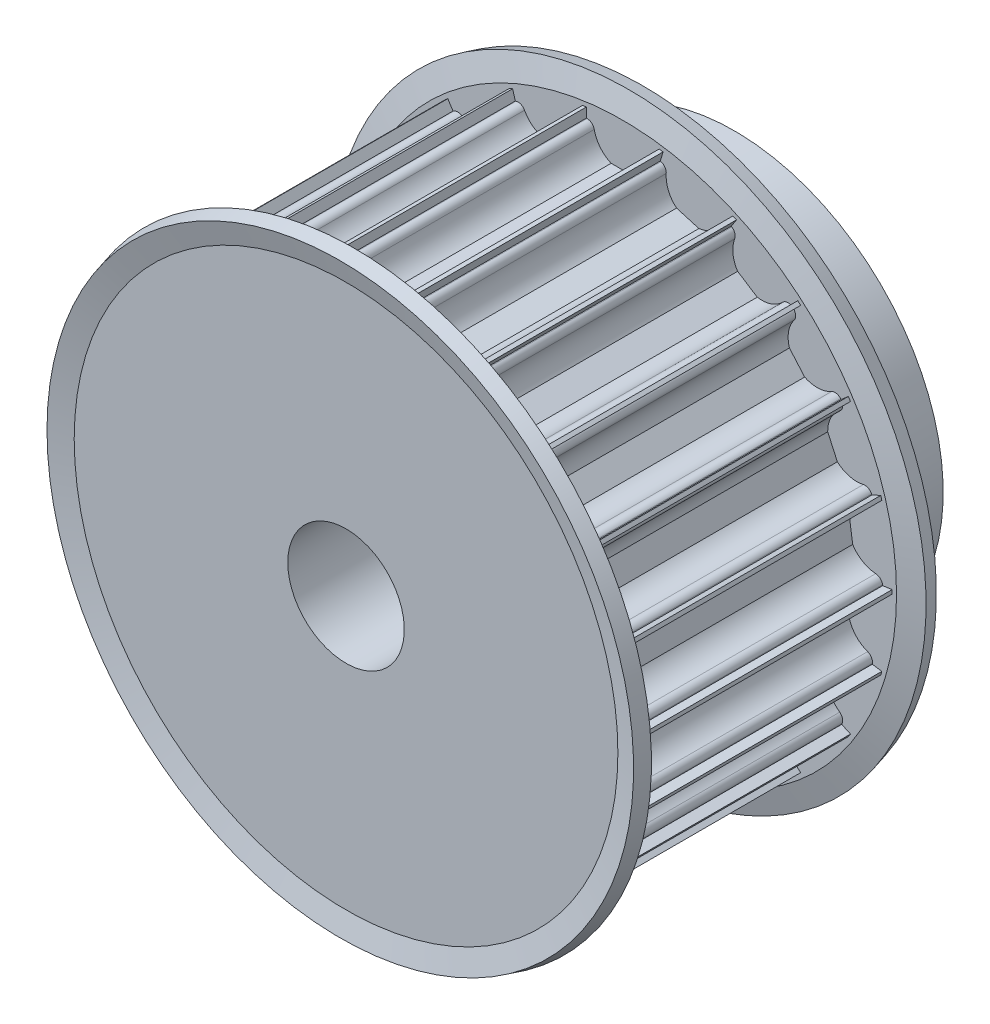
SolidWorks part; units mm, degrees
ref_plane "Front Plane" through (0, 0, 0) normal (0, 0, 1) x (1, 0, 0)
ref_plane "Top Plane" through (0, 0, 0) normal (0, 1, 0) x (1, 0, 0)
ref_plane "Right Plane" through (0, 0, 0) normal (1, 0, 0) x (0, 0, -1)
ref_axis "Axis1" through (0, 0, -88.99) along (0, 0, 1)
sketch "Sketch1" plane through (0, 0, 0) normal (1, 0, 0) x (0, 0, -1)
  line L0 (0, 6) -> (0, 27.75)
  line L1 (0, 27.75) -> (30, 27.75)
  line L2 (30, 27.75) -> (30, 21.5)
  line L3 (30, 21.5) -> (40, 21.5)
  line L4 (40, 21.5) -> (40, 6)
  line L5 (40, 6) -> (0, 6)
  line L6 (88.99, 0) -> (-88.99, 0) construction
  dimension "D1" = 21.75
  dimension "D2" = 30
  dimension "D3" = 10
  dimension "D4" = 15.5
  dimension "D5" = 6
revolve "Revolve1" add sketch "Sketch1" angle 360 about axis through (0, 0, -88.99) along (0, 0, 1)
sketch "Sketch2" plane through (0, 0, 0) normal (0, 0, 1) x (1, 0, 0)
  line L0 (3.6742, 26.5) -> (3.75, 26.5)
  line L1 (-3.75, 28.5) -> (3.75, 28.5)
  line L2 (-3.75, 28.5) -> (-3.75, 26.5)
  line L3 (-3.75, 26.5) -> (-3.6742, 26.5)
  line L4 (3.75, 28.5) -> (3.75, 26.5)
  line L5 (-1.199, 23.75) -> (1.199, 23.75)
  arc A0 (-2.9394, 25.9) -> (-1.199, 23.75) centre (0, 26.5) ccw
  arc A1 (-2.9394, 25.9) -> (-3.6742, 26.5) centre (-3.6742, 25.75) ccw
  arc A2 (2.9394, 25.9) -> (3.6742, 26.5) centre (3.6742, 25.75) cw
  arc A3 (1.199, 23.75) -> (2.9394, 25.9) centre (0, 26.5) ccw
  dimension "D1" = 3
  dimension "D5" = 0.75
  dimension "D6" = 0.75
  dimension "D2" = 2
  dimension "D3" = 7.5
  dimension "D4" = 26.5
  dimension "D7" = 2.75
extrude "Cut-Extrude1" cut sketch "Sketch2" against normal through all
pattern_circular "CirPattern1" count 22 over 360 about axis through (0, 0, 0) along (0, 0, 1) of "Cut-Extrude1"
sketch "Sketch4" plane through (0, 0, 0) normal (1, 0, 0) x (0, 0, -1)
  line L0 (0, 25.679) -> (0, 23.1257) construction
  line L1 (0, 23.1955) -> (1.5, 23.1955)
  line L2 (0, 23.1955) -> (0, 28.1955)
  line L3 (0, 28.1955) -> (1.5, 28.1955) construction
  line L4 (1.5, 23.1955) -> (1.5, 28.1955)
  line L5 (1.5, 28.1955) -> (0.0511, 27.8072) construction
  line L6 (1.5, 28.1955) -> (0.8569, 30.5955)
  line L7 (0.0511, 27.8072) -> (-0.592, 30.2072)
  line L8 (0.8569, 30.5955) -> (-0.592, 30.2072)
  line L9 (15, 27.4382) -> (15, -27.4955) construction
  line L10 (30, 27.4382) -> (0, 27.4382) construction
  line L11 (30, -27.4955) -> (0, -27.4955) construction
  line L12 (29.1431, 30.5955) -> (30.592, 30.2072)
  line L13 (29.9489, 27.8072) -> (30.592, 30.2072)
  line L14 (28.5, 28.1955) -> (29.1431, 30.5955)
  line L15 (28.5, 28.1955) -> (29.9489, 27.8072) construction
  line L16 (28.5, 23.1955) -> (28.5, 28.1955)
  line L17 (30, 28.1955) -> (28.5, 28.1955) construction
  line L18 (30, 23.1955) -> (30, 28.1955)
  line L19 (30, 23.1955) -> (28.5, 23.1955)
  dimension "D1" = 1.5
  dimension "D2" = 5
  dimension "D3" = 1.5
  dimension "D4" = 165
  dimension "D5" = 2.4
  dimension "D6" = 0.7
revolve "Revolve2" add sketch "Sketch4" angle 360 about axis through (0, 0, -88.99) along (0, 0, 1)
